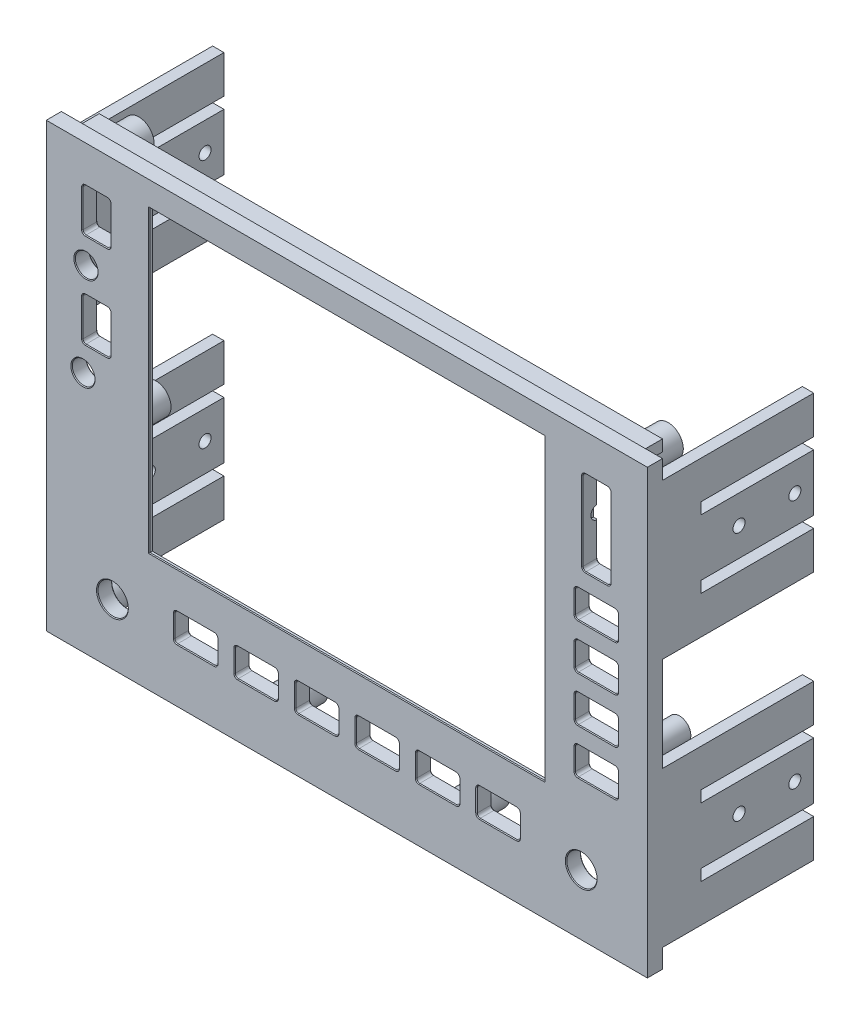
SolidWorks part; units mm, degrees
ref_plane "Plan de face" through (0, 0, 0) normal (0, 0, 1) x (1, 0, 0)
ref_plane "Plan de dessus" through (0, 0, 0) normal (0, 1, 0) x (1, 0, 0)
ref_plane "Plan de droite" through (0, 0, 0) normal (1, 0, 0) x (0, 0, -1)
sketch "Esquisse1" plane through (0, 0, 0) normal (0, 0, 1) x (1, 0, 0)
  line L1 (0, 0) -> (160, 0)
  line L2 (0, 0) -> (0, 117)
  line L3 (0, 117) -> (160, 117)
  line L4 (160, 0) -> (160, 117)
  dimension "D1" = 160
  dimension "D2" = 117
extrude "Boss.-Extru.1" add sketch "Esquisse1" along normal blind 4
sketch "Esquisse3" plane through (0, 0, 4) normal (0, 0, 1) x (1, 0, 0)
  line L1 (27.75, 110.5) -> (132.25, 110.5)
  line L2 (27.75, 110.5) -> (27.75, 31.5)
  line L3 (27.75, 31.5) -> (132.25, 31.5)
  line L4 (132.25, 110.5) -> (132.25, 31.5)
  line L7 (160, 0) -> (160, 117) construction
  line L8 (0, 117) -> (0, 0) construction
  line L9 (160, 117) -> (0, 117) construction
  dimension "D1" = 104.5
  dimension "D2" = 79
  dimension "D3" = 27.75
  dimension "D4" = 27.75
  dimension "D5" = 6.5
extrude "Enlèv. mat.-Extru.2" cut sketch "Esquisse3" against normal blind 4
sketch "Esquisse14" plane through (0, 0, 0) normal (0, 0, -1) x (-1, 0, 0)
  line L0 (-160, 0) -> (-160, 117) construction
  line L1 (-159.5, 5) -> (-156.5, 5)
  line L2 (-159.5, 5) -> (-159.5, 46)
  line L3 (-159.5, 46) -> (-156.5, 46)
  line L4 (-156.5, 5) -> (-156.5, 46)
  line L5 (0, 0) -> (-160, 0) construction
  line L6 (-159.5, 112) -> (-156.5, 112)
  line L7 (-159.5, 112) -> (-159.5, 71)
  line L8 (-159.5, 71) -> (-156.5, 71)
  line L9 (-156.5, 112) -> (-156.5, 71)
  line L10 (-160, 117) -> (0, 117) construction
  line L11 (0, 117) -> (0, 0) construction
  line L12 (-0.5, 46) -> (-3.5, 46)
  line L13 (-0.5, 46) -> (-0.5, 5)
  line L14 (-0.5, 5) -> (-3.5, 5)
  line L15 (-3.5, 46) -> (-3.5, 5)
  line L17 (-0.5, 112) -> (-3.5, 112)
  line L18 (-0.5, 112) -> (-0.5, 71)
  line L19 (-0.5, 71) -> (-3.5, 71)
  line L20 (-3.5, 112) -> (-3.5, 71)
  dimension "D1" = 3
  dimension "D2" = 3
  dimension "D3" = 41
  dimension "D4" = 41
  dimension "D5" = 5
  dimension "D6" = 5
  dimension "D7" = 3
  dimension "D8" = 41
  dimension "D9" = 3
  dimension "D10" = 41
  dimension "D11" = 5
  dimension "D12" = 5
  dimension "D13" = 0.5
  dimension "D14" = 0.5
  dimension "D15" = 0.5
  dimension "D16" = 0.5
extrude "Boss.-Extru.3" add sketch "Esquisse14" along normal blind 40
sketch "Esquisse15" plane through (160, 0, 0) normal (1, 0, 0) x (0, 0, -1)
  line L0 (40, 112) -> (40, 71) construction
  line L1 (40, 102) -> (10.2487, 102)
  line L2 (40, 102) -> (40, 99)
  line L3 (40, 99) -> (10.2487, 99)
  line L4 (10.2487, 102) -> (10.2487, 99)
  line L5 (40, 46) -> (40, 5) construction
  line L6 (40, 84) -> (10.2487, 84)
  line L7 (40, 84) -> (40, 81)
  line L8 (40, 81) -> (10.2487, 81)
  line L9 (10.2487, 84) -> (10.2487, 81)
  line L10 (40, 36) -> (10.2487, 36)
  line L11 (40, 36) -> (40, 33)
  line L12 (40, 33) -> (10.2487, 33)
  line L13 (10.2487, 36) -> (10.2487, 33)
  line L14 (40, 71) -> (0, 71) construction
  line L15 (40, 18) -> (10.2487, 18)
  line L16 (40, 18) -> (40, 15)
  line L17 (40, 15) -> (10.2487, 15)
  line L18 (10.2487, 18) -> (10.2487, 15)
  line L19 (40, 5) -> (0, 5) construction
  line L20 (40, 46) -> (0, 46) construction
  line L21 (40, 112) -> (0, 112) construction
  circle A0 centre (35, 91.5) radius 1.6
  circle A1 centre (35, 25.5) radius 1.6
  circle A2 centre (20.2487, 91.5) radius 1.6
  circle A3 centre (20.2487, 25.5) radius 1.6
  dimension "D11" = 3.2
  dimension "D12" = 3.2
  dimension "D13" = 3.2
  dimension "D14" = 3.2
  dimension "D1" = 3
  dimension "D2" = 3
  dimension "D3" = 15
  dimension "D4" = 10
  dimension "D5" = 3
  dimension "D6" = 3
  dimension "D7" = 15
  dimension "D8" = 10
  dimension "D9" = 10
  dimension "D10" = 10
  dimension "D15" = 7.5
  dimension "D16" = 7.5
  dimension "D17" = 7.5
  dimension "D18" = 7.5
  dimension "D19" = 10
  dimension "D20" = 10
  dimension "D21" = 5
  dimension "D22" = 5
extrude "Enlèv. mat.-Extru.8" cut sketch "Esquisse15" against normal through all
sketch "Esquisse16" plane through (0, 0, 4) normal (0, 0, 1) x (1, 0, 0)
  line L0 (0, 117) -> (0, 0) construction
  line L1 (0.5, 125.5977) -> (-30.5716, 125.5977)
  line L2 (0.5, 125.5977) -> (0.5, -6.5823)
  line L3 (0.5, -6.5823) -> (-30.5716, -6.5823)
  line L4 (-30.5716, 125.5977) -> (-30.5716, -6.5823)
  line L5 (159.5, 127.2773) -> (172.0966, 127.2773)
  line L6 (159.5, 127.2773) -> (159.5, -8.7657)
  line L7 (159.5, -8.7657) -> (172.0966, -8.7657)
  line L8 (172.0966, 127.2773) -> (172.0966, -8.7657)
  line L9 (160, 0) -> (160, 117) construction
  dimension "D1" = 0.5
  dimension "D2" = 0.5
extrude "Enlèv. mat.-Extru.9" cut sketch "Esquisse16" against normal through all
sketch "Esquisse9" plane through (0, 0, 0) normal (0, 0, -1) x (-1, 0, 0)
  line L0 (-132.25, 31.5) -> (-132.25, 110.5) construction
  line L1 (-139.25, 113) -> (-20.75, 113)
  line L2 (-139.25, 113) -> (-139.25, 24)
  line L3 (-139.25, 24) -> (-20.75, 24)
  line L4 (-20.75, 113) -> (-20.75, 24)
  line L5 (-27.75, 110.5) -> (-27.75, 31.5) construction
  line L6 (-27.75, 31.5) -> (-132.25, 31.5) construction
  line L7 (-132.25, 110.5) -> (-27.75, 110.5) construction
  dimension "D1" = 7
  dimension "D2" = 7
  dimension "D3" = 7.5
  dimension "D4" = 2.5
  dimension "D5" = 118.5
  dimension "D6" = 89
extrude "Enlèv. mat.-Extru.5" cut sketch "Esquisse9" against normal blind 3
sketch "Esquisse4" plane through (0, 0, 4) normal (0, 0, 1) x (1, 0, 0)
  line L0 (159.5, 0) -> (159.5, 5) construction
  line L2 (0.5, 5) -> (0.5, 0) construction
  line L4 (0.5, 0) -> (159.5, 0) construction
  circle A0 centre (142, 16) radius 4
  circle A1 centre (18, 16) radius 4
  dimension "D1" = 8
  dimension "D2" = 8
  dimension "D4" = 17.5
  dimension "D5" = 16
  dimension "D6" = 16
  dimension "D7" = 17.5
extrude "Enlèv. mat.-Extru.3" cut sketch "Esquisse4" against normal blind 4
sketch "Esquisse12" plane through (0, 0, 0) normal (0, 0, -1) x (-1, 0, 0)
  line L2 (-0.5, 0) -> (-159.5, 0) construction
  line L3 (-159.5, 117) -> (-0.5, 117) construction
  line L4 (-159.5, 46) -> (-159.5, 71) construction
  line L5 (-159.5, 112) -> (-159.5, 117) construction
  line L6 (-159.5, 0) -> (-159.5, 5) construction
  line L7 (-0.5, 71) -> (-0.5, 46) construction
  line L8 (-0.5, 5) -> (-0.5, 0) construction
  line L9 (-159.5, 117) -> (-0.5, 117) construction
  line L11 (-0.5, 117) -> (-0.5, 112) construction
  circle A0 centre (-152, 8) radius 1.425
  circle A1 centre (-152, 8) radius 4
  circle A2 centre (-8, 8) radius 1.425
  circle A3 centre (-8, 8) radius 4
  circle A4 centre (-104, 8) radius 1.425
  circle A5 centre (-104, 8) radius 4
  circle A6 centre (-56, 8) radius 1.425
  circle A7 centre (-56, 8) radius 4
  circle A8 centre (-150, 111) radius 1.425
  circle A9 centre (-150, 111) radius 4
  circle A10 centre (-10, 111) radius 1.425
  circle A11 centre (-10, 111) radius 4
  circle A12 centre (-153, 70.3123) radius 1.425
  circle A13 centre (-153, 70.3123) radius 3
  circle A14 centre (-152.9997, 46.3123) radius 1.425
  circle A15 centre (-152.9997, 46.3123) radius 3
  circle A16 centre (-14.5, 52.8) radius 1.425
  circle A17 centre (-14.5, 52.8) radius 4
  dimension "D1" = 2.85
  dimension "D2" = 2.85
  dimension "D3" = 8
  dimension "D4" = 8
  dimension "D9" = 2.85
  dimension "D10" = 2.85
  dimension "D11" = 8
  dimension "D12" = 8
  dimension "D18" = 8
  dimension "D19" = 2.85
  dimension "D22" = 2.85
  dimension "D23" = 8
  dimension "D26" = 2.85
  dimension "D27" = 6
  dimension "D29" = 2.85
  dimension "D30" = 6
  dimension "D31" = 2.85
  dimension "D35" = 8
  dimension "D5" = 7.5
  dimension "D6" = 9.5
  dimension "D7" = 8
  dimension "D8" = 8
  dimension "D13" = 48
  dimension "D14" = 48
  dimension "D15" = 48
  dimension "D16" = 8
  dimension "D17" = 8
  dimension "D20" = 6
  dimension "D21" = 6.5
  dimension "D24" = 6
  dimension "D28" = 40.6877
  dimension "D32" = 24
  dimension "D33" = 6.5003
  dimension "D34" = 9.5
  dimension "D36" = 14
  dimension "D37" = 7.5
  dimension "D38" = 64.2
extrude "Boss.-Extru.2" add sketch "Esquisse12" along normal blind 11 separate body contours A9 A8 | A13 A12 | A15 A14 | A1 A0 | A5 A4 | A7 A6 | A3 A2 | A17 A16 | A11 A10
sketch "Esquisse10" plane through (0, 0, 0) normal (0, 0, -1) x (-1, 0, 0)
  line L0 (-172.9105, 18) -> (39.4334, 18) construction
  line L1 (-159.5, 117) -> (-0.5, 117) construction
  line L2 (-124.9, 21.7) -> (-115.1, 21.7)
  line L3 (-125.7, 20.9) -> (-125.7, 15.1)
  line L4 (-124.9, 14.3) -> (-115.1, 14.3)
  line L5 (-114.3, 20.9) -> (-114.3, 15.1)
  line L6 (-108.9, 21.7) -> (-99.1, 21.7)
  line L7 (-109.7, 20.9) -> (-109.7, 15.1)
  line L8 (-108.9, 14.3) -> (-99.1, 14.3)
  line L9 (-98.3, 20.9) -> (-98.3, 15.1)
  line L10 (-92.9, 21.7) -> (-83.1, 21.7)
  line L11 (-93.7, 20.9) -> (-93.7, 15.1)
  line L12 (-92.9, 14.3) -> (-83.1, 14.3)
  line L13 (-82.3, 20.9) -> (-82.3, 15.1)
  line L14 (-76.9, 21.7) -> (-67.1, 21.7)
  line L15 (-77.7, 20.9) -> (-77.7, 15.1)
  line L16 (-76.9, 14.3) -> (-67.1, 14.3)
  line L17 (-66.3, 20.9) -> (-66.3, 15.1)
  line L18 (-60.9, 21.7) -> (-51.1, 21.7)
  line L19 (-61.7, 20.9) -> (-61.7, 15.1)
  line L20 (-60.9, 14.3) -> (-51.1, 14.3)
  line L21 (-50.3, 20.9) -> (-50.3, 15.1)
  line L22 (-44.9, 21.7) -> (-35.1, 21.7)
  line L23 (-45.7, 20.9) -> (-45.7, 15.1)
  line L24 (-44.9, 14.3) -> (-35.1, 14.3)
  line L25 (-34.3, 20.9) -> (-34.3, 15.1)
  line L27 (-0.5, 0) -> (-159.5, 0) construction
  line L28 (-146, 118.9934) -> (-146, 24.726) construction
  line L29 (-40, 28.2834) -> (-40, 3.035) construction
  line L30 (-148.9, 107.2) -> (-143.1, 107.2)
  line L31 (-149.7, 106.4) -> (-149.7, 85.6)
  line L32 (-148.9, 84.8) -> (-143.1, 84.8)
  line L33 (-142.3, 106.4) -> (-142.3, 85.6)
  line L34 (-0.5, 117) -> (-0.5, 112) construction
  line L35 (-13.75, 118.9934) -> (-13.75, 30.4767) construction
  line L36 (-150.9, 80.2) -> (-141.1, 80.2)
  line L37 (-151.7, 79.4) -> (-151.7, 73.6)
  line L38 (-150.9, 72.8) -> (-141.1, 72.8)
  line L39 (-140.3, 79.4) -> (-140.3, 73.6)
  line L40 (-150.9, 68.2) -> (-141.1, 68.2)
  line L41 (-151.7, 67.4) -> (-151.7, 61.6)
  line L42 (-150.9, 60.8) -> (-141.1, 60.8)
  line L43 (-140.3, 67.4) -> (-140.3, 61.6)
  line L44 (-150.9, 56.2) -> (-141.1, 56.2)
  line L45 (-151.7, 55.4) -> (-151.7, 49.6)
  line L46 (-150.9, 48.8) -> (-141.1, 48.8)
  line L47 (-140.3, 55.4) -> (-140.3, 49.6)
  line L48 (-150.9, 44.2) -> (-141.1, 44.2)
  line L49 (-151.7, 43.4) -> (-151.7, 37.6)
  line L50 (-150.9, 36.8) -> (-141.1, 36.8)
  line L51 (-140.3, 43.4) -> (-140.3, 37.6)
  line L52 (-0.5, 5) -> (-0.5, 0) construction
  line L53 (-159.5, 0) -> (-159.5, 5) construction
  line L54 (-56, 28.2834) -> (-56, 3.035) construction
  line L55 (-16.65, 107.2) -> (-10.85, 107.2)
  line L56 (-17.45, 106.4) -> (-17.45, 96.6)
  line L57 (-16.65, 95.8) -> (-10.85, 95.8)
  line L58 (-10.05, 106.4) -> (-10.05, 96.6)
  line L59 (-16.65, 82.2) -> (-10.85, 82.2)
  line L60 (-17.45, 81.4) -> (-17.45, 71.6)
  line L61 (-16.65, 70.8) -> (-10.85, 70.8)
  line L62 (-10.05, 81.4) -> (-10.05, 71.6)
  line L63 (-72, 28.2834) -> (-72, 3.035) construction
  line L64 (-88, 28.2834) -> (-88, 3.035) construction
  line L65 (-104, 28.2834) -> (-104, 3.035) construction
  line L66 (-120, 28.2834) -> (-120, 3.035) construction
  line L67 (-137.0477, 40.5) -> (-155.6204, 40.5) construction
  line L68 (-136.7264, 52.5) -> (-156.211, 52.5) construction
  line L69 (-135.9662, 64.5) -> (-155.9414, 64.5) construction
  line L70 (-136.1586, 76.5) -> (-155.6204, 76.5) construction
  line L71 (-138.5123, 101.5) -> (-156.7912, 101.5) construction
  line L72 (-138.5123, 90.5) -> (-156.7912, 90.5) construction
  line L73 (-3.3273, 101.5) -> (-26.2396, 101.5) construction
  line L74 (-2.1726, 89) -> (-22.743, 89) construction
  line L75 (-11, 89.5154) -> (-11, 81.8674) construction
  line L76 (-2.1726, 76.5) -> (-24.6945, 76.5) construction
  line L77 (-2.1726, 64) -> (-24.3071, 64) construction
  line L78 (-159.5, 112) -> (-159.5, 117) construction
  arc A0 (-45.7, 15.1) -> (-44.9, 14.3) centre (-44.9, 15.1) ccw
  arc A1 (-35.1, 21.7) -> (-34.3, 20.9) centre (-35.1, 20.9) cw
  arc A2 (-35.1, 14.3) -> (-34.3, 15.1) centre (-35.1, 15.1) ccw
  arc A3 (-44.9, 21.7) -> (-45.7, 20.9) centre (-44.9, 20.9) ccw
  arc A4 (-51.1, 21.7) -> (-50.3, 20.9) centre (-51.1, 20.9) cw
  arc A5 (-51.1, 14.3) -> (-50.3, 15.1) centre (-51.1, 15.1) ccw
  arc A6 (-61.7, 15.1) -> (-60.9, 14.3) centre (-60.9, 15.1) ccw
  arc A7 (-60.9, 21.7) -> (-61.7, 20.9) centre (-60.9, 20.9) ccw
  arc A8 (-67.1, 21.7) -> (-66.3, 20.9) centre (-67.1, 20.9) cw
  arc A9 (-67.1, 14.3) -> (-66.3, 15.1) centre (-67.1, 15.1) ccw
  arc A10 (-77.7, 15.1) -> (-76.9, 14.3) centre (-76.9, 15.1) ccw
  arc A11 (-76.9, 21.7) -> (-77.7, 20.9) centre (-76.9, 20.9) ccw
  arc A12 (-83.1, 21.7) -> (-82.3, 20.9) centre (-83.1, 20.9) cw
  arc A13 (-83.1, 14.3) -> (-82.3, 15.1) centre (-83.1, 15.1) ccw
  arc A14 (-93.7, 15.1) -> (-92.9, 14.3) centre (-92.9, 15.1) ccw
  arc A15 (-92.9, 21.7) -> (-93.7, 20.9) centre (-92.9, 20.9) ccw
  arc A16 (-99.1, 21.7) -> (-98.3, 20.9) centre (-99.1, 20.9) cw
  arc A17 (-99.1, 14.3) -> (-98.3, 15.1) centre (-99.1, 15.1) ccw
  arc A18 (-109.7, 15.1) -> (-108.9, 14.3) centre (-108.9, 15.1) ccw
  arc A19 (-108.9, 21.7) -> (-109.7, 20.9) centre (-108.9, 20.9) ccw
  arc A20 (-115.1, 21.7) -> (-114.3, 20.9) centre (-115.1, 20.9) cw
  arc A21 (-115.1, 14.3) -> (-114.3, 15.1) centre (-115.1, 15.1) ccw
  arc A22 (-125.7, 15.1) -> (-124.9, 14.3) centre (-124.9, 15.1) ccw
  arc A23 (-124.9, 21.7) -> (-125.7, 20.9) centre (-124.9, 20.9) ccw
  arc A24 (-150.9, 44.2) -> (-151.7, 43.4) centre (-150.9, 43.4) ccw
  arc A25 (-151.7, 37.6) -> (-150.9, 36.8) centre (-150.9, 37.6) ccw
  arc A26 (-141.1, 36.8) -> (-140.3, 37.6) centre (-141.1, 37.6) ccw
  arc A27 (-141.1, 44.2) -> (-140.3, 43.4) centre (-141.1, 43.4) cw
  arc A28 (-141.1, 56.2) -> (-140.3, 55.4) centre (-141.1, 55.4) cw
  arc A29 (-141.1, 48.8) -> (-140.3, 49.6) centre (-141.1, 49.6) ccw
  arc A30 (-151.7, 49.6) -> (-150.9, 48.8) centre (-150.9, 49.6) ccw
  arc A31 (-150.9, 56.2) -> (-151.7, 55.4) centre (-150.9, 55.4) ccw
  arc A32 (-150.9, 68.2) -> (-151.7, 67.4) centre (-150.9, 67.4) ccw
  arc A33 (-151.7, 61.6) -> (-150.9, 60.8) centre (-150.9, 61.6) ccw
  arc A34 (-141.1, 60.8) -> (-140.3, 61.6) centre (-141.1, 61.6) ccw
  arc A35 (-141.1, 68.2) -> (-140.3, 67.4) centre (-141.1, 67.4) cw
  arc A36 (-141.1, 72.8) -> (-140.3, 73.6) centre (-141.1, 73.6) ccw
  arc A37 (-141.1, 80.2) -> (-140.3, 79.4) centre (-141.1, 79.4) cw
  arc A38 (-151.7, 73.6) -> (-150.9, 72.8) centre (-150.9, 73.6) ccw
  arc A39 (-150.9, 80.2) -> (-151.7, 79.4) centre (-150.9, 79.4) ccw
  arc A40 (-149.7, 85.6) -> (-148.9, 84.8) centre (-148.9, 85.6) ccw
  arc A41 (-143.1, 84.8) -> (-142.3, 85.6) centre (-143.1, 85.6) ccw
  arc A42 (-143.1, 107.2) -> (-142.3, 106.4) centre (-143.1, 106.4) cw
  arc A43 (-148.9, 107.2) -> (-149.7, 106.4) centre (-148.9, 106.4) ccw
  circle A44 centre (-11, 89) radius 3
  circle A45 centre (-10.2, 64) radius 3
  arc A46 (-10.85, 82.2) -> (-10.05, 81.4) centre (-10.85, 81.4) cw
  arc A47 (-10.85, 70.8) -> (-10.05, 71.6) centre (-10.85, 71.6) ccw
  arc A48 (-17.45, 71.6) -> (-16.65, 70.8) centre (-16.65, 71.6) ccw
  arc A49 (-16.65, 82.2) -> (-17.45, 81.4) centre (-16.65, 81.4) ccw
  arc A50 (-10.85, 95.8) -> (-10.05, 96.6) centre (-10.85, 96.6) ccw
  arc A51 (-10.85, 107.2) -> (-10.05, 106.4) centre (-10.85, 106.4) cw
  arc A52 (-16.65, 107.2) -> (-17.45, 106.4) centre (-16.65, 106.4) ccw
  arc A53 (-17.45, 96.6) -> (-16.65, 95.8) centre (-16.65, 96.6) ccw
  point P34 (-45.7, 14.3)
  point P39 (-34.3, 14.3)
  point P46 (-50.3, 14.3)
  point P49 (-61.7, 14.3)
  point P56 (-66.3, 14.3)
  point P59 (-77.7, 14.3)
  point P66 (-82.3, 14.3)
  point P69 (-93.7, 14.3)
  point P76 (-98.3, 14.3)
  point P79 (-109.7, 14.3)
  point P116 (-151.7, 44.2)
  point P119 (-151.7, 36.8)
  point P138 (-140.3, 60.8)
  point P141 (-140.3, 68.2)
  point P178 (-10.05, 82.2)
  point P181 (-10.05, 70.8)
  dimension "D27" = 0.8
  dimension "D43" = 0.8
  dimension "D59" = 6
  dimension "D62" = 6
  dimension "D64" = 0.8
  dimension "D30" = 39.5
  dimension "D1" = 3.7
  dimension "D2" = 3.7
  dimension "D3" = 11.4
  dimension "D4" = 11.4
  dimension "D5" = 11.4
  dimension "D6" = 11.4
  dimension "D7" = 11.4
  dimension "D8" = 11.4
  dimension "D9" = 3.7
  dimension "D10" = 3.7
  dimension "D11" = 3.7
  dimension "D12" = 3.7
  dimension "D13" = 3.7
  dimension "D14" = 3.7
  dimension "D15" = 3.7
  dimension "D16" = 3.7
  dimension "D17" = 3.7
  dimension "D18" = 3.7
  dimension "D19" = 13.5
  dimension "D20" = 16
  dimension "D21" = 16
  dimension "D22" = 16
  dimension "D23" = 16
  dimension "D24" = 39.5
  dimension "D26" = 18
  dimension "D28" = 3.7
  dimension "D29" = 3.7
  dimension "D32" = 5.7
  dimension "D33" = 5.7
  dimension "D34" = 12
  dimension "D35" = 14
  dimension "D36" = 5.7
  dimension "D37" = 15.5
  dimension "D38" = 12
  dimension "D39" = 12
  dimension "D40" = 3.55
  dimension "D41" = 22.5
  dimension "D42" = 13.25
  dimension "D45" = 5.7
  dimension "D46" = 5.7
  dimension "D47" = 5.7
  dimension "D48" = 5.7
  dimension "D50" = 5.7
  dimension "D51" = 3.7
  dimension "D52" = 3.7
  dimension "D53" = 5.7
  dimension "D55" = 12.5
  dimension "D56" = 3.7
  dimension "D57" = 3.7
  dimension "D58" = 16
  dimension "D60" = 5.7
  dimension "D61" = 2.75
  dimension "D65" = 5.7
  dimension "D66" = 5.7
  dimension "D67" = 5.7
  dimension "D68" = 5.7
  dimension "D69" = 5.7
  dimension "D70" = 5.7
  dimension "D71" = 5.7
  dimension "D72" = 5.7
  dimension "D73" = 5.7
  dimension "D74" = 5.7
  dimension "D75" = 5.7
  dimension "D76" = 5.7
  dimension "D77" = 3.7
  dimension "D78" = 3.7
  dimension "D79" = 3.7
  dimension "D80" = 3.7
  dimension "D81" = 3.7
  dimension "D82" = 3.7
  dimension "D83" = 3.7
  dimension "D84" = 3.7
  dimension "D85" = 5.7
  dimension "D86" = 5.7
  dimension "D87" = 11
  dimension "D88" = 5.7
  dimension "D89" = 5.7
  dimension "D90" = 12.5
  dimension "D91" = 12.5
extrude "Enlèv. mat.-Extru.6" cut sketch "Esquisse10" against normal blind 4 and the other way blind 30
sketch "Esquisse11" plane through (149.7, 0, 0) normal (-1, 0, 0) x (0, 0, 1)
  line L0 (0, 106.4) -> (0, 85.6) construction
  line L1 (4, 107.2) -> (0, 107.2) construction
  line L2 (4, 84.8) -> (0, 84.8) construction
  circle A0 centre (0, 96.2) radius 1.75
  dimension "D1" = 3.5
  dimension "D2" = 11
  dimension "D3" = 11.4
extrude "Enlèv. mat.-Extru.7" cut sketch "Esquisse11" against normal blind 1.5 and the other way blind 8.5
chamfer "Chanfrein2" distance 0.2 angle 45 227 edges at (80, 110.5, 4) (146, 84.8, 4) (142.5343, 85.0343, 4) (149.4657, 85.0343, 4) (142.3, 96, 4) (149.7, 96, 4) (142.5343, 106.9657, 4) (149.4657, 106.9657, 4) (146, 107.2, 4) (146, 68.2, 4) (151.4657, 67.9657, 4) (140.5343, 67.9657, 4) (151.7, 64.5, 4) (140.3, 64.5, 4) (151.4657, 61.0343, 4) (140.5343, 61.0343, 4) (146, 60.8, 4) (146, 56.2, 4) (151.4657, 55.9657, 4) (140.5343, 55.9657, 4) (151.7, 52.5, 4) (140.3, 52.5, 4) (151.4657, 49.0343, 4) (140.5343, 49.0343, 4) (146, 48.8, 4) (146, 44.2, 4) (151.4657, 43.9657, 4) (140.5343, 43.9657, 4) (151.7, 40.5, 4) (140.3, 40.5, 4) (151.4657, 37.0343, 4) (140.5343, 37.0343, 4) (146, 36.8, 4) (146, 16, 4) (88, 14.3, 4) (82.5343, 14.5343, 4) (93.4657, 14.5343, 4) (82.3, 18, 4) (93.7, 18, 4) (82.5343, 21.4657, 4) (93.4657, 21.4657, 4) (88, 21.7, 4) (104, 14.3, 4) (98.5343, 14.5343, 4) (109.4657, 14.5343, 4) (98.3, 18, 4) (109.7, 18, 4) (98.5343, 21.4657, 4) (109.4657, 21.4657, 4) (104, 21.7, 4) (120, 14.3, 4) (114.5343, 14.5343, 4) (125.4657, 14.5343, 4) (114.3, 18, 4) (125.7, 18, 4) (114.5343, 21.4657, 4) (125.4657, 21.4657, 4) (120, 21.7, 4) (72, 14.3, 4) (66.5343, 14.5343, 4) (77.4657, 14.5343, 4) (66.3, 18, 4) (77.7, 18, 4) (66.5343, 21.4657, 4) (77.4657, 21.4657, 4) (72, 21.7, 4) (56, 14.3, 4) (50.5343, 14.5343, 4) (61.4657, 14.5343, 4) (50.3, 18, 4) (61.7, 18, 4) (50.5343, 21.4657, 4) (61.4657, 21.4657, 4) (56, 21.7, 4) (40, 14.3, 4) (34.5343, 14.5343, 4) (45.4657, 14.5343, 4) (34.3, 18, 4) (45.7, 18, 4) (34.5343, 21.4657, 4) (45.4657, 21.4657, 4) (40, 21.7, 4) (22, 16, 4) (7.2, 64, 4) (13.75, 70.8, 4) (10.2843, 71.0343, 4) (17.2157, 71.0343, 4) (10.05, 76.5, 4) (17.45, 76.5, 4) (10.2843, 81.9657, 4) (17.2157, 81.9657, 4) (13.75, 82.2, 4) (8, 89, 4) (13.75, 95.8, 4) (10.2843, 96.0343, 4) (17.2157, 96.0343, 4) (10.05, 101.5, 4) (17.45, 101.5, 4) (10.2843, 106.9657, 4) (17.2157, 106.9657, 4) (13.75, 107.2, 4) (8, 89, 0) (7.2, 64, 0) (13.75, 82.2, 0) (17.2157, 81.9657, 0) (10.2843, 81.9657, 0) (17.45, 76.5, 0) (10.05, 76.5, 0) (17.2157, 71.0343, 0) (10.2843, 71.0343, 0) (13.75, 70.8, 0) (13.75, 107.2, 0) (17.2157, 106.9657, 0) (17.45, 101.5, 0) (10.05, 101.5, 0) (17.2157, 96.0343, 0) (10.2843, 96.0343, 0) (13.75, 95.8, 0) (27.75, 71, 3) (80, 31.5, 3) (132.25, 71, 3) (80, 110.5, 3) (20.75, 68.5, 0) (80, 113, 0) (80, 24, 0) (139.25, 68.5, 0) (120, 14.3, 0) (114.5343, 14.5343, 0) (125.4657, 14.5343, 0) (114.3, 18, 0) (125.7, 18, 0) (114.5343, 21.4657, 0) (125.4657, 21.4657, 0) (120, 21.7, 0) (104, 14.3, 0) (98.5343, 14.5343, 0) (109.4657, 14.5343, 0) (98.3, 18, 0) (109.7, 18, 0) (98.5343, 21.4657, 0) (109.4657, 21.4657, 0) (104, 21.7, 0) (88, 14.3, 0) (82.5343, 14.5343, 0) (93.4657, 14.5343, 0) (82.3, 18, 0) (93.7, 18, 0) (82.5343, 21.4657, 0) (93.4657, 21.4657, 0) (88, 21.7, 0) (72, 14.3, 0) (66.5343, 14.5343, 0) (77.4657, 14.5343, 0) (66.3, 18, 0) (77.7, 18, 0) (66.5343, 21.4657, 0) (77.4657, 21.4657, 0) (72, 21.7, 0) (56, 14.3, 0) (50.5343, 14.5343, 0) (61.4657, 14.5343, 0) (50.3, 18, 0) (61.7, 18, 0) (50.5343, 21.4657, 0) (61.4657, 21.4657, 0) (56, 21.7, 0) (40, 21.7, 0) (45.4657, 21.4657, 0) (34.5343, 21.4657, 0) (45.7, 18, 0) (34.3, 18, 0) (45.4657, 14.5343, 0) (34.5343, 14.5343, 0) (40, 14.3, 0) (22, 16, 0) (146, 16, 0) (151.7, 40.5, 0) (151.4657, 37.0343, 0) (146, 36.8, 0) (140.5343, 37.0343, 0) (140.3, 40.5, 0) (140.5343, 43.9657, 0) (146, 44.2, 0) (146, 48.8, 0) (140.5343, 49.0343, 0) (140.3, 52.5, 0) (151.7, 52.5, 0) (140.5343, 55.9657, 0) (151.4657, 55.9657, 0) (146, 56.2, 0) (151.7, 64.5, 0) (151.4657, 61.0343, 0) (146, 60.8, 0) (140.5343, 61.0343, 0) (140.3, 64.5, 0) (140.5343, 67.9657, 0) (146, 68.2, 0) (146, 72.8, 0) (140.5343, 73.0343, 0) (140.3, 76.5, 0) (151.7, 76.5, 0) (140.5343, 79.9657, 0) (151.4657, 79.9657, 0) (146, 80.2, 0) (146, 107.2, 0) (142.5343, 106.9657, 0) (142.3, 102.175, 0) (149.7, 102.175, 0) (149.7, 90.025, 0) (142.3, 90.025, 0) (149.4657, 85.0343, 0) (142.5343, 85.0343, 0) (146, 84.8, 0) (146, 80.2, 4) (151.4657, 79.9657, 4) (140.5343, 79.9657, 4) (151.7, 76.5, 4) (140.3, 76.5, 4) (151.4657, 73.0343, 4) (140.5343, 73.0343, 4) (146, 72.8, 4) (10.2843, 106.9657, 0) (151.4657, 43.9657, 0) (151.4657, 49.0343, 0) (151.4657, 67.9657, 0) (151.4657, 73.0343, 0) (149.4657, 106.9657, 0)
chamfer "Chanfrein3" distance 0.2 angle 45 3 edges at (132.25, 71.1, 4) (80, 31.5, 4) (27.75, 71.1, 4)
sketch "Esquisse17" plane through (0, 0, 0) normal (0, 0, -1) x (-1, 0, 0)
  line L0 (-0.5, 0) -> (-159.5, 0) construction
  line L1 (-154.5, 0.5) -> (-5.5, 0.5)
  line L2 (-154.5, 0.5) -> (-154.5, 4.5)
  line L3 (-154.5, 4.5) -> (-5.5, 4.5)
  line L4 (-5.5, 0.5) -> (-5.5, 4.5)
  line L6 (-0.5, 5) -> (-0.5, 0) construction
  line L7 (-159.5, 117) -> (-0.5, 117) construction
  line L8 (-154.5, 116.5) -> (-5.5, 116.5)
  line L9 (-154.5, 116.5) -> (-154.5, 113.5)
  line L10 (-154.5, 113.5) -> (-5.5, 113.5)
  line L11 (-5.5, 116.5) -> (-5.5, 113.5)
  line L12 (-159.5, 112) -> (-159.5, 117) construction
  line L13 (-0.5, 117) -> (-0.5, 112) construction
  line L14 (-159.5, 0) -> (-159.5, 5) construction
  dimension "D1" = 0.5
  dimension "D2" = 5
  dimension "D3" = 5
  dimension "D4" = 4
  dimension "D5" = 0.5
  dimension "D6" = 3
  dimension "D7" = 5
  dimension "D8" = 5
extrude "Boss.-Extru.4" add sketch "Esquisse17" along normal blind 5
